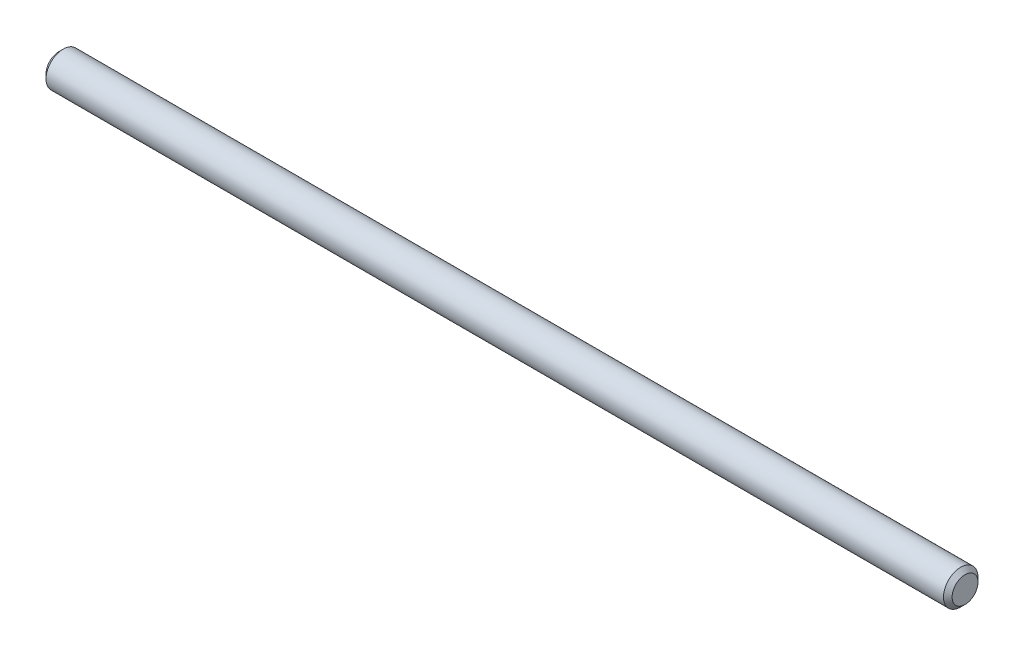
SolidWorks part; units mm, degrees
ref_plane "Front Plane" through (0, 0, 0) normal (0, 0, 1) x (1, 0, 0)
ref_plane "Top Plane" through (0, 0, 0) normal (0, 1, 0) x (1, 0, 0)
ref_plane "Right Plane" through (0, 0, 0) normal (1, 0, 0) x (0, 0, -1)
sketch "Sketch1" plane through (0, 0, 0) normal (1, 0, 0) x (0, 0, -1)
  circle A0 centre (0, 0) radius 2
  dimension "D1" = 4
extrude "Boss-Extrude1" add sketch "Sketch1" along normal mid plane 105
cosmetic thread "Cosmetic Thread1" parameters "D1"=8, "D2"=3.22
cosmetic thread "Cosmetic Thread2" parameters "D1"=8, "D2"=3.22
chamfer "Chamfer1" distance 0.5 angle 45 2 edges at (-52.5, 0, -2) (52.5, 0, -2)
